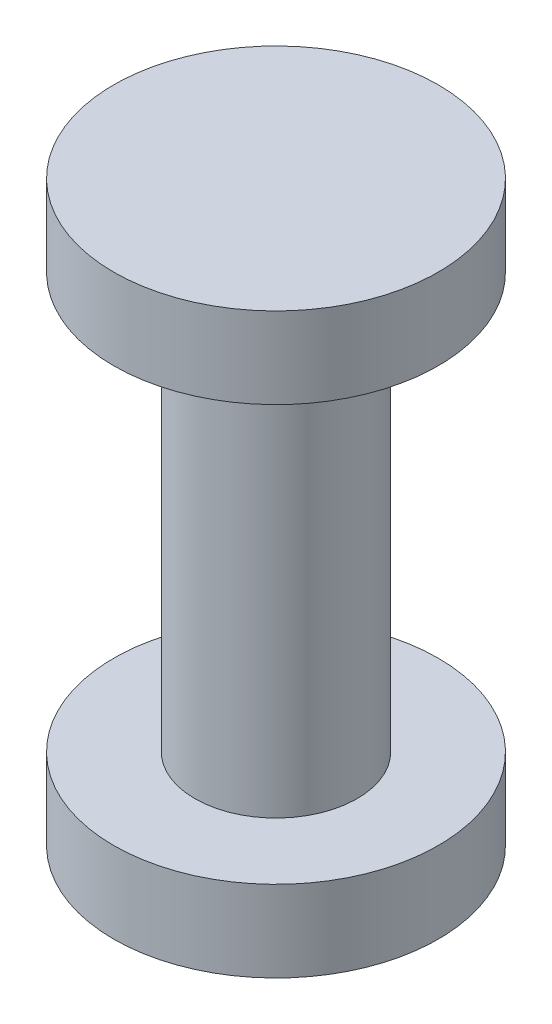
SolidWorks part; units mm, degrees
material "Acrylic (Medium-high impact)"
ref_plane "Front Plane" through (0, 0, 0) normal (0, 0, 1) x (1, 0, 0)
ref_plane "Top Plane" through (0, 0, 0) normal (0, 1, 0) x (1, 0, 0)
ref_plane "Right Plane" through (0, 0, 0) normal (1, 0, 0) x (0, 0, -1)
sketch "Sketch1" plane through (0, 0, 0) normal (0, 1, 0) x (1, 0, 0)
  circle A0 centre (0, 0) radius 2.5
extrude "Boss-Extrude1" add sketch "Sketch1" along normal blind 12.8
sketch "Sketch2" plane through (0, 12.8, 0) normal (0, 1, 0) x (1, 0, 0)
  circle A0 centre (0, 0) radius 5
extrude "Boss-Extrude2" add sketch "Sketch2" along normal blind 2.5
sketch "Sketch3" plane through (0, 0, 0) normal (0, -1, 0) x (-1, 0, 0)
  circle A0 centre (0, 0) radius 5
extrude "Boss-Extrude3" add sketch "Sketch3" along normal blind 2.5
